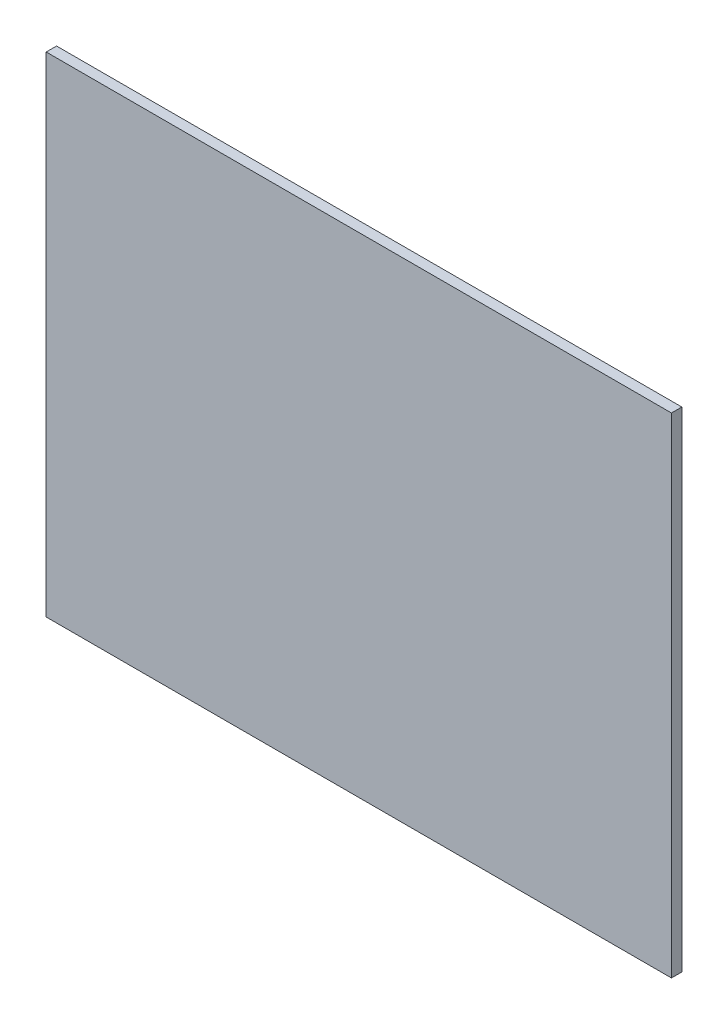
SolidWorks part; units mm, degrees
ref_plane "Front Plane" through (0, 0, 0) normal (0, 0, 1) x (1, 0, 0)
ref_plane "Top Plane" through (0, 0, 0) normal (0, 1, 0) x (1, 0, 0)
ref_plane "Right Plane" through (0, 0, 0) normal (1, 0, 0) x (0, 0, -1)
sketch "Sketch1" plane through (0, 0, 0) normal (0, 0, 1) x (1, 0, 0)
  line L1 (0, 0) -> (1150, 0)
  line L2 (0, 0) -> (0, -900)
  line L3 (0, -900) -> (1150, -900)
  line L4 (1150, 0) -> (1150, -900)
  dimension "D1" = 1150
  dimension "D2" = 900
extrude "Boss-Extrude1" add sketch "Sketch1" along normal blind 19.05
